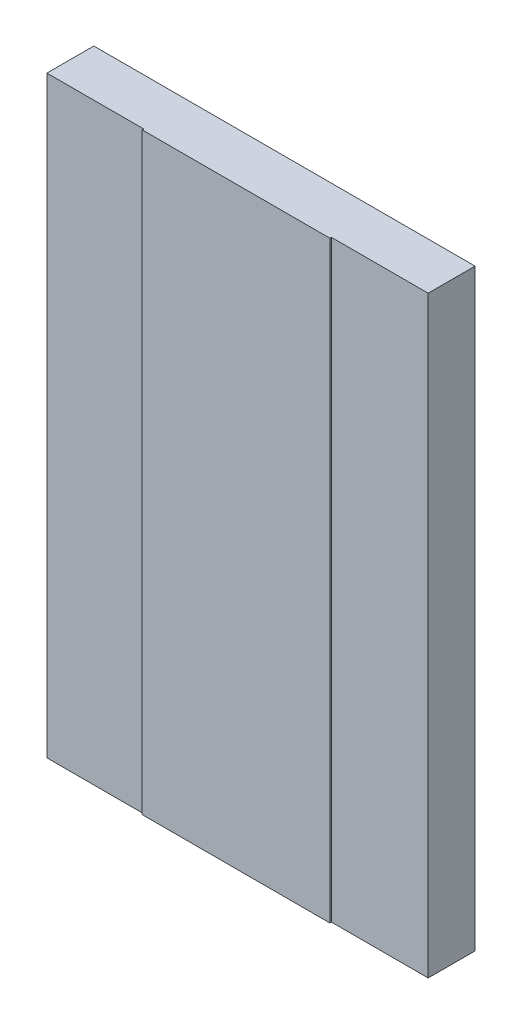
SolidWorks part; units mm, degrees
ref_plane "Front Plane" through (0, 0, 0) normal (0, 0, 1) x (1, 0, 0)
ref_plane "Top Plane" through (0, 0, 0) normal (0, 1, 0) x (1, 0, 0)
ref_plane "Right Plane" through (0, 0, 0) normal (1, 0, 0) x (0, 0, -1)
sketch "Sketch1" plane through (0, 0, 0) normal (0, 0, 1) x (1, 0, 0)
  line L1 (-50.0063, 77.7875) -> (50.0062, 77.7875)
  line L2 (-50.0063, 77.7875) -> (-50.0062, -77.7875)
  line L3 (-50.0062, -77.7875) -> (50.0062, -77.7875)
  line L4 (50.0062, 77.7875) -> (50.0062, -77.7875)
  line L5 (-50.0063, 77.7875) -> (50.0062, -77.7875) construction
  line L6 (-50.0062, -77.7875) -> (50.0062, 77.7875) construction
  point P0 (0, 0)
  dimension "D1" = 100.0125
  dimension "D2" = 155.575
extrude "Boss-Extrude1" add sketch "Sketch1" along normal mid plane 12.7
sketch "Sketch2" plane through (0, 0, 6.35) normal (0, 0, 1) x (1, 0, 0)
  line L0 (0, 77.7875) -> (0, -77.7875) construction
  line L1 (50.0062, 77.7875) -> (-50.0063, 77.7875) construction
  line L2 (-50.0062, -77.7875) -> (50.0062, -77.7875) construction
sketch "Sketch3" plane through (0, 0, -6.35) normal (0, 0, -1) x (-1, 0, 0)
  line L0 (0, 77.7875) -> (0, -77.7875) construction
  line L1 (-50.0062, 77.7875) -> (50.0063, 77.7875) construction
  line L2 (50.0062, -77.7875) -> (-50.0062, -77.7875) construction
sketch "Sketch4" plane through (0, 77.7875, 0) normal (0, 1, 0) x (1, 0, 0)
  line L1 (-50.0063, -6.35) -> (-24.6063, -6.35)
  line L2 (-50.0063, -6.35) -> (-50.0063, -5.9531)
  line L3 (-50.0063, -5.9531) -> (-24.6063, -5.9531)
  line L4 (-24.6063, -6.35) -> (-24.6063, -5.9531)
  line L5 (50.0062, -6.35) -> (24.6062, -6.35)
  line L6 (50.0062, -6.35) -> (50.0062, -5.9531)
  line L7 (50.0062, -5.9531) -> (24.6062, -5.9531)
  line L8 (24.6062, -6.35) -> (24.6062, -5.9531)
  dimension "D1" = 25.4
  dimension "D2" = 25.4
  dimension "D3" = 0.3969
  dimension "D4" = 0.3969
extrude "Cut-Extrude1" cut sketch "Sketch4" against normal up to next
